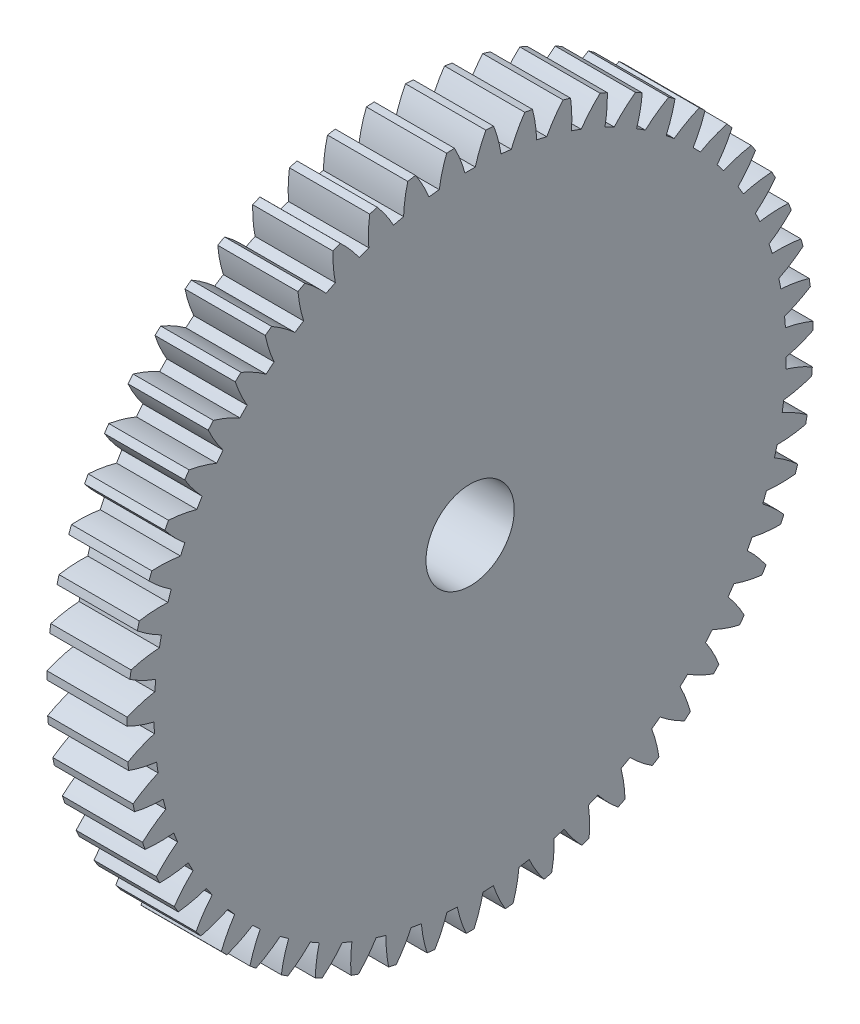
SolidWorks part; units mm, degrees
ref_plane "Plane1" through (0, 0, 0) normal (0, 0, 1) x (1, 0, 0)
ref_plane "Plane2" through (0, 0, 0) normal (0, 1, 0) x (1, 0, 0)
ref_plane "Plane3" through (0, 0, 0) normal (1, 0, 0) x (0, 0, -1)
sketch "HoldingSke" plane through (0, 0, 0) normal (0, 1, 0) x (1, 0, 0)
  line L0 (0, 0) -> (0.3824, -0.5461)
  line L1 (-15, 0) -> (100, 0) construction
  line L2 (0, 0) -> (-2.1039, 2.3779)
  line L3 (0, 0) -> (-11.863, 4.5341)
  line L4 (0, 0) -> (4.9534, 7.0742)
  line L5 (0, 0) -> (-23.4238, -8.7364)
  line L6 (0, 0) -> (-8.2896, -5.593)
  line L7 (-2.1039, 2.3779) -> (3.2774, 26.7919)
  line L8 (-76.2, 54.61) -> (-73.9, 54.61)
  line L9 (-71.009, 38.7566) -> (-53.1078, 45.2721)
  line L10 (-76.2, 71.12) -> (104.1128, 71.12)
  line L11 (0, 0) -> (-10, 0)
  line L12 (-76.2, 101.6) -> (-76.147, 101.6)
  line L13 (24.9733, 27.94) -> (52.9518, 28.4284)
  line L14 (24.9733, 27.94) -> (24.9743, 27.94)
  line L15 (24.9733, 27.94) -> (100.4006, 29.5858)
  line L16 (-63.627, -1.5) -> (-12.827, -1.5)
  circle A0 centre (0, 0) radius 6
  circle A1 centre (0, 0) radius 14
  circle A2 centre (0, 0) radius 14
  circle A3 centre (0, 0) radius 6
  dimension "MHD" = 28
  dimension "Hub_dia" = 28
  dimension "Bore" = 12
  dimension "MBD" = 12
  dimension "Num_teeth" = 55
  dimension "Pitch" = 0.6667
  dimension "Overall_len" = 25
  dimension "Show_teeth" = 55
  dimension "Thickness" = 10
  dimension "OAL" = 25.0001
  dimension "T_dim" = 2.3
  dimension "Ap" = 20
  dimension "H" = 19.05
  dimension "Pitch_radius" = 180.3128
  dimension "Width" = 10
  dimension "Backlash" = 0.053
  dimension "Addendum_fac" = 1
  dimension "Dedendum_fac" = 1.25
  dimension "Clearance_fac" = 0.25
  dimension "Dedendum_add" = 0.001
  dimension "Module" = 1.5
sketch "BasProSke" plane through (0, 0, 0) normal (0, 1, 0) x (1, 0, 0)
  line L0 (-10, 0) -> (60, 0) construction
  line L1 (0, 0) -> (0, 42.75)
  line L2 (0, 0) -> (10, 0)
  line L3 (10, 0) -> (10, 42.75)
  line L4 (10, 42.75) -> (0, 42.75)
  dimension "Thickness" = 10
  dimension "Diameter" = 85.5
revolve "Base-Revolve" add sketch "BasProSke" angle 360 about L0
sketch "TooCutSke" plane through (0, 0, 0) normal (1, 0, 0) x (0, 0, -1)
  line L1 (0, 0) -> (0, 107) construction
  line L2 (0, 0) -> (-1.2707, 41.2304) construction
  line L3 (0, 0) -> (-4.7082, 82.3369) construction
  line L4 (-1.2707, 41.2304) -> (-2.3541, 41.1685) construction
  arc A0 (0.6438, 39.3687) -> (-0.6438, 39.3687) centre (0, 0) ccw
  arc A1 (1.9666, 42.7302) -> (-1.9666, 42.7302) centre (0, 0) ccw
  circle A2 centre (0, 0) radius 41.25 construction
  circle A3 centre (0, 0) radius 38.7623 construction
  arc A4 (-0.6438, 39.3687) -> (-1.9666, 42.7302) centre (-16.5669, 35.0436) ccw
  arc A5 (1.9666, 42.7302) -> (0.6438, 39.3687) centre (16.5669, 35.0436) ccw
  dimension "Root_dia" = 78.748
  dimension "Overcut_dia" = 85.5508
  dimension "Pitch_dia" = 82.5
  dimension "Base_dia" = 77.5246
  dimension "Flank_rad" = 16.5
  dimension "Half_ang" = 3.273
  dimension "Half_CT" = 1.0852
extrude "ToothCut" cut sketch "TooCutSke" along normal through all
fillet "Breaks" [suppressed] radius 0.03
fillet "RootFillets" [suppressed] radius 0.376
pattern_circular "TeethCuts" count 55 every 6.545 about axis through (-10, 0, 0) along (1, 0, 0) of "ToothCut", "RootFillets", "Breaks"
sketch "HubNeaOneSke" plane through (0, 0, 0) normal (-1, 0, 0) x (0, 0, 1)
  circle A0 centre (0, 0) radius 14
  dimension "Diameter" = 28
extrude "HubNearOne" add sketch "HubNeaOneSke" along normal blind 15.0001
sketch "HubNeaBotSke" plane through (0, 0, 0) normal (-1, 0, 0) x (0, 0, 1)
  circle A0 centre (0, 0) radius 14
  dimension "Diameter" = 28
extrude "HubNearBoth" [suppressed] add sketch "HubNeaBotSke" along normal blind 7.5
ref_plane "FarPln" through (10, 0, 0) normal (1, 0, 0) x (0, 0, -1)
sketch "HubFarSke" plane through (10, 0, 0) normal (1, 0, 0) x (0, 0, -1)
  circle A0 centre (0, 0) radius 14
  dimension "Diameter" = 28
extrude "HubFar" [suppressed] add sketch "HubFarSke" along normal blind 7.5
sketch "BorSke" plane through (0, 0, 0) normal (1, 0, 0) x (0, 0, -1)
  circle A0 centre (0, 0) radius 6
  dimension "Diameter" = 12
extrude "Bore" cut sketch "BorSke" along normal mid plane 50.0001
sketch "KeySke" plane through (0, 0, 0) normal (1, 0, 0) x (0, 0, -1)
  line L0 (-2.5, 0) -> (-2.5, 8.3)
  line L1 (-2.5, 8.3) -> (2.5, 8.3)
  line L2 (2.5, 8.3) -> (2.5, 0)
  line L3 (0, 0) -> (0, 34) construction
  line L4 (-2.5, 0) -> (2.5, 0)
  dimension "Offset" = 8.3
  dimension "Width" = 5
extrude "Keyway" [suppressed] cut sketch "KeySke" along normal mid plane 50.0001
pattern_circular "Keyway2" [suppressed] count 2 every 90 about axis through (-10, 0, 0) along (1, 0, 0)
sketch "Çizim1" plane through (-15.0001, 0, 0) normal (-1, 0, 0) x (0, 0, 1)
  circle A0 centre (0, 0) radius 14
  circle A1 centre (0, 0) radius 11
  dimension "D1" = 22
extrude "Kes-Ekstrüzyon1" cut sketch "Çizim1" against normal up to surface (15.0001 mm away) up to face at (0, 0, -14)
sketch "Çizim2" plane through (-15.0001, 0, 0) normal (-1, 0, 0) x (0, 0, 1)
  circle A0 centre (0, 0) radius 6
  circle A1 centre (0, 0) radius 5.5
  dimension "D1" = 11
extrude "Yükseklik-Ekstrüzyon1" add sketch "Çizim2" against normal up to surface (25.0001 mm away) up to face at (10, 0, 6)
equation "' \"Module@HoldingSke\" = 6.35"
equation "' \"Num_teeth@HoldingSke\" = 12"
equation "' \"Ap@HoldingSke\" =  20"
equation "' \"Ap@HoldingSke\" = 20"
equation "' \"Width@HoldingSke\" = 0.5 * 25.4"
equation "' \"Hub_dia@HoldingSke\"= 1 * 25.4"
equation "' \"Hub_dia@HoldingSke\" = 1 * 25.4"
equation "' \"Overall_len@HoldingSke\" = 1.0 * 25.4"
equation "' \"Bore@HoldingSke\" = 0.75 * 25.4"
equation "' \"T_dim@HoldingSke\" = 0.1 * 25.4"
equation "' \"Width@KeySke\" = 0.25 * 25.4"
equation "' \"Show_teeth@HoldingSke\" = 13"
equation "' \"Backlash@HoldingSke\" = 0.009 * 25.4"
equation "' \"Addendum_fac@HoldingSke\" = 1.0"
equation "' \"Dedendum_fac@HoldingSke\" = 1.25"
equation "' \"Dedendum_add@HoldingSke\" = 0.00005 * 25.4"
equation "' \"Clearance_fac@HoldingSke\" = 0.25"
equation "\"Pitch@HoldingSke\" = 1 / \"Module@HoldingSke\""
equation "\"Overcut_dia@TooCutSke\" = (\"Num_teeth@HoldingSke\" + 2 * \"Addendum_fac@HoldingSke\") / \"Pitch@HoldingSke\" + 0.002 * 25.4"
equation "\"Pitch_dia@TooCutSke\" = \"Num_teeth@HoldingSke\" / \"Pitch@HoldingSke\""
equation "\"Base_dia@TooCutSke\" = \"Num_teeth@HoldingSke\" / \"Pitch@HoldingSke\" * cos((\"Ap@HoldingSke\"  * 3.14159265 / 180))"
equation "\"Root_dia@TooCutSke\" = (\"Num_teeth@HoldingSke\" + 2) / \"Pitch@HoldingSke\" - 2 * (\"Addendum_fac@HoldingSke\" + \"Dedendum_fac@HoldingSke\") / \"Pitch@HoldingSke\" - \"Dedendum_add@HoldingSke\" * 2"
equation "\"Half_ang@TooCutSke\" = 180 / \"Num_teeth@HoldingSke\""
equation "\"Half_CT@TooCutSke\" = \"Num_teeth@HoldingSke\" / \"Pitch@HoldingSke\" * sin((3.14159265 / 2 / \"Num_teeth@HoldingSke\")) / 2 - 7 * \"Backlash@HoldingSke\" / 4"
equation "\"Flank_rad@TooCutSke\" = \"Num_teeth@HoldingSke\" / \"Pitch@HoldingSke\" / 5"
equation "\"Radius@RootFillets\" = \"Clearance_fac@HoldingSke\" / \"Pitch@HoldingSke\" + \"Dedendum_add@HoldingSke\""
equation "\"Break_rad@Breaks\" = 0.02 / \"Pitch@HoldingSke\""
equation "\"Thickness@HoldingSke\" = \"Width@HoldingSke\""
equation "\"OAL@HoldingSke\" = \"Thickness@HoldingSke\""
equation "\"MHD@HoldingSke\" = (\"Num_teeth@HoldingSke\" + 2) / \"Pitch@HoldingSke\" - 2 * (\"Addendum_fac@HoldingSke\" + \"Dedendum_fac@HoldingSke\")  / \"Pitch@HoldingSke\" - \"Dedendum_add@HoldingSke\" * 2"
equation "\"MBD@HoldingSke\" = (\"Num_teeth@HoldingSke\" + 2) / \"Pitch@HoldingSke\" - 2 * (\"Addendum_fac@HoldingSke\" + \"Dedendum_fac@HoldingSke\")  / \"Pitch@HoldingSke\" - \"Dedendum_add@HoldingSke\" * 2 - 0.002 * 25.4"
equation "\"MHD@HoldingSke\" = ((sgn( \"MHD@HoldingSke\" - \"Hub_dia@HoldingSke\" )-1)*( \"MHD@HoldingSke\" - \"Hub_dia@HoldingSke\" ))/-2+ \"Hub_dia@HoldingSke\""
equation "\"MBD@HoldingSke\" = ((sgn( \"MBD@HoldingSke\" - \"Bore@HoldingSke\" )-1)*( \"MBD@HoldingSke\" - \"Bore@HoldingSke\" ))/-2+ \"Bore@HoldingSke\""
equation "\"OAL@HoldingSke\" = ((sgn( \"OAL@HoldingSke\" - \"Overall_len@HoldingSke\" )+1)*( \"OAL@HoldingSke\" - \"Overall_len@HoldingSke\" ))/2 + \"Overall_len@HoldingSke\" + 0.000002 * 25.4"
equation "\"Num_teeth@TeethCuts\" = int( \"Show_teeth@HoldingSke\" ) + 1"
equation "\"Num_teeth@TeethCuts\" = ((sgn( \"Num_teeth@TeethCuts\" - \"Num_teeth@HoldingSke\" )-1)*( \"Num_teeth@TeethCuts\" - \"Num_teeth@HoldingSke\" ))/-2+ \"Num_teeth@HoldingSke\""
equation "\"Num_teeth@TeethCuts\" = ((sgn( \"Num_teeth@TeethCuts\" - 2.0)+1)*( \"Num_teeth@TeethCuts\" - 2.0))/2 +2.0"
equation "\"Angle@TeethCuts\" = 360.0 / \"Num_teeth@HoldingSke\""
equation "\"Diameter@BasProSke\" = (\"Num_teeth@HoldingSke\" + 2 * \"Addendum_fac@HoldingSke\") / \"Pitch@HoldingSke\""
equation "\"Thickness@BasProSke\"  = \"Thickness@HoldingSke\""
equation "' \"Fillet_rad@BasProSke\" =  \"Thickness@HoldingSke\" * 0.05"
equation "' \"Fillet_rad@BasProSke\" = \"Thickness@HoldingSke\" * 0.05"
equation "\"MHD@HoldingSke\" = ((sgn( \"MHD@HoldingSke\" - \"Root_dia@TooCutSke\" )-1)*( \"MHD@HoldingSke\" - \"Root_dia@TooCutSke\" ))/-2+ \"Root_dia@TooCutSke\""
equation "\"Diameter@HubNeaOneSke\" = \"MHD@HoldingSke\""
equation "\"Length@HubNearOne\" = \"OAL@HoldingSke\" - \"Thickness@BasProSke\""
equation "\"Diameter@HubNeaBotSke\" = \"MHD@HoldingSke\""
equation "\"Length@HubNearBoth\" = ( \"OAL@HoldingSke\" - \"Thickness@BasProSke\" ) / 2.0"
equation "\"Thickness@FarPln\" = \"Thickness@BasProSke\""
equation "\"Diameter@HubFarSke\" = \"MHD@HoldingSke\""
equation "\"Length@HubFar\" = ( \"OAL@HoldingSke\" - \"Thickness@BasProSke\" ) / 2.0"
equation "\"Diameter@BorSke\" = \"MBD@HoldingSke\""
equation "\"D1@Bore\" = \"OAL@HoldingSke\" * 2.0"
equation "\"D1@Keyway\" = \"OAL@HoldingSke\" * 2.0"
equation "\"Offset@KeySke\" = \"T_dim@HoldingSke\" + \"MBD@HoldingSke\" / 2.0"
